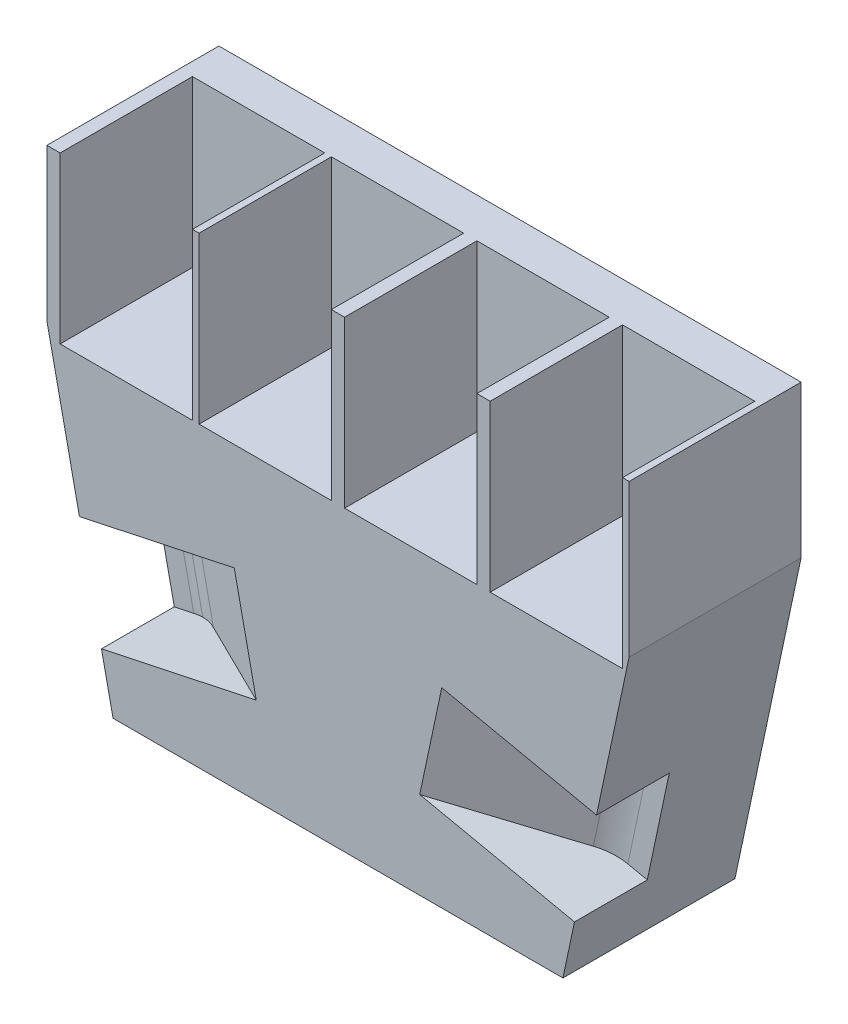
SolidWorks part; units mm, degrees
ref_plane "Front" through (0, 0, 0) normal (0, 0, 1) x (1, 0, 0)
ref_plane "Top" through (0, 0, 0) normal (0, 1, 0) x (1, 0, 0)
ref_plane "Right" through (0, 0, 0) normal (1, 0, 0) x (0, 0, -1)
sketch "草图1" plane through (0, 0, 0) normal (0, 0, 1) x (1, 0, 0)
  line L0 (-34, -24) -> (34, -24)
  line L1 (-44, 46) -> (44, 46)
  line L2 (-44, 46) -> (-44, 23)
  line L4 (44, 46) -> (44, 23)
  line L5 (-66.7553, 0) -> (86.3051, 0) construction
  line L8 (-44, 23) -> (-34, -24)
  line L9 (-44, 23) -> (56.7889, 23) construction
  line L10 (34, -24) -> (44, 23)
  dimension "D1" = 88
  dimension "D3" = 44
  dimension "D4" = 68
  dimension "D5" = 34
  dimension "D6" = 24
extrude "凸台-拉伸1" add sketch "草图1" along normal blind 26
sketch "草图2" plane through (-37.4127, -7.9602, 0) normal (-0.9781, -0.2081, 0) x (0, 0, 1)
  line L0 (13, -16.3989) -> (13, 31.6532) construction
  line L1 (26, -16.3989) -> (0, -16.3989) construction
  line L2 (26, 31.6532) -> (0, 31.6532) construction
  line L3 (0, 0) -> (26, 0)
  line L4 (26, 31.6532) -> (26, -16.3989) construction
sketch "草图3" plane through (0, 0, 0) normal (0, 0, -1) x (-1, 0, 0)
  line L0 (0, -24) -> (0, 47.0389) construction
  line L1 (34, -24) -> (-34, -24) construction
  line L3 (-20, -24) -> (20, -24)
  line L4 (-20, -24) -> (-20, 12)
  line L5 (-20, 12) -> (20, 12)
  line L6 (20, -24) -> (20, 12)
  dimension "D1" = 36
  dimension "D2" = 40
  dimension "D3" = 20
extrude "切除-拉伸4" cut sketch "草图3" against normal blind 20
sketch "草图4" plane through (0, 46, 0) normal (0, 1, 0) x (1, 0, 0)
  line L0 (44, -26) -> (-44, -26) construction
  line L1 (43, -26) -> (23, -26)
  line L2 (43, -26) -> (43, -6)
  line L3 (43, -6) -> (23, -6)
  line L4 (23, -26) -> (23, -6)
  line L5 (44, -26) -> (44, 0) construction
  line L6 (21, -26) -> (1, -26)
  line L7 (21, -26) -> (21, -6)
  line L8 (21, -6) -> (1, -6)
  line L9 (1, -26) -> (1, -6)
  line L10 (-1, -26) -> (-21, -26)
  line L11 (-1, -26) -> (-1, -6)
  line L12 (-1, -6) -> (-21, -6)
  line L13 (-21, -26) -> (-21, -6)
  line L14 (-22, -26) -> (-42, -26)
  line L15 (-22, -26) -> (-22, -6)
  line L16 (-22, -6) -> (-42, -6)
  line L17 (-42, -26) -> (-42, -6)
  dimension "D1" = 20
  dimension "D2" = 21
  dimension "D3" = 20
  dimension "D4" = 20
  dimension "D5" = 20
  dimension "D6" = 2
  dimension "D7" = 2
  dimension "D8" = 20
  dimension "D9" = 20
  dimension "D10" = 20
  dimension "D11" = 21
  dimension "D12" = 20
extrude "切除-拉伸5" cut sketch "草图4" against normal blind 25
sketch3d "3D草图5"
  line L0 (-37.3866, -7.9546, 26.004) -> (-19.9225, -4.2388, 26.004) construction
  line L1 (-37.4127, -7.9602, 0) -> (-37.4127, -7.9602, 26) construction
  line L2 (-37.3866, -7.9546, 26.004) -> (-37.4127, -7.9602, 12.8891) construction
  line L3 (-26.6334, -5.6667, 23.004) -> (-26.6334, -5.6667, 31.004)
  line L4 (-26.6334, -5.6667, 31.004) -> (-34.4583, -7.3315, 31.004)
  arc A0 (-26.6334, -5.6667, 23.004) -> (-34.4583, -7.3315, 31.004) centre (-34.4583, -7.3315, 23.004) ccw
  point P2 (-36.1231, 0.4933, 23.004)
  dimension "D1" = 3
  dimension "D2" = 3
extrude "切除-拉伸3" cut sketch "3D草图5" along direction (0.2081, -0.9781, 0) on the side against the normal mid plane 16
sketch "草图6" plane through (37.4127, -7.9602, 0) normal (0.9781, -0.2081, 0) x (0, 0, -1)
  line L0 (0, 0) -> (-26, 0)
  line L1 (-26, -16.3989) -> (-26, 31.6532) construction
sketch3d "3D草图6"
  line L0 (37.4127, -7.9602, 0) -> (37.4127, -7.9602, 26) construction
  line L2 (37.4127, -7.9602, 26) -> (26.6536, -5.671, 25.9966) construction
  line L3 (34.4784, -7.3358, 14.9991) -> (44.8243, -9.5371, 14.9991)
  line L4 (34.4784, -7.3358, 29) -> (44.8243, -9.5371, 29)
  line L5 (44.8243, -9.5371, 29) -> (44.8243, -9.5371, 14.9991)
  line L6 (26.6536, -5.671, 22.9991) -> (26.6536, -5.671, 29)
  line L7 (26.6536, -5.671, 29) -> (34.4784, -7.3358, 29)
  arc A0 (34.4784, -7.3358, 14.9991) -> (26.6536, -5.671, 22.9991) centre (34.4784, -7.3358, 22.9991) ccw
  point P2 (36.1433, 0.489, 22.9991)
  dimension "D1" = 3
  dimension "D2" = 3
extrude "切除-拉伸6" cut sketch "3D草图6" along direction (0.2081, 0.9781, 0) on the side against the normal mid plane 16
sketch "草图7" plane through (-1.6649, 7.8248, 0) normal (0.2081, -0.9781, 0) x (0.9781, 0.2081, 0)
  line L0 (-38.2502, 0) -> (-38.2502, 26) construction
  line L1 (-38.2502, 26) -> (28.261, 26) construction
  line L2 (-38.2502, 26) -> (-29.5933, 17.3431) construction
  line L3 (-24.5567, 20) -> (-31.2008, 16.1005)
  line L4 (-24.5567, 20) -> (-10.0872, 28.4922)
  line L5 (-10.0872, 28.4922) -> (-33.6713, 30.8426)
  line L6 (-35.2502, 15) -> (-43.2502, 15)
  line L7 (-43.2502, 15) -> (-43.2502, 23)
  arc A0 (-35.2502, 15) -> (-31.2008, 16.1005) centre (-35.2502, 23) ccw
  arc A1 (-33.6713, 30.8426) -> (-43.2502, 23) centre (-35.2502, 23) ccw
  dimension "D3" = 16
  dimension "D1" = 3
  dimension "D2" = 3
extrude "切除-拉伸7" cut sketch "草图7" along normal blind 16
sketch "草图11" plane through (-1.6649, -7.8248, 0) normal (0.2081, 0.9781, 0) x (0.9781, -0.2081, 0)
  line L0 (-28.261, -26) -> (38.2502, -26) construction
  line L1 (38.2502, 0) -> (38.2502, -26) construction
  line L2 (24.5567, -20) -> (31.2008, -16.1005) construction
  line L3 (31.2008, -16.1005) -> (14.3336, -26)
  line L4 (14.3336, -26) -> (32.6666, -30.5713)
  line L5 (35.2502, -15) -> (38.2502, -14.9991)
  line L6 (38.2502, -14.9991) -> (40.4608, -16.9296)
  arc A0 (32.6666, -30.5713) -> (40.4608, -16.9296) centre (35.2502, -23) ccw
  arc A1 (35.2502, -15) -> (31.2008, -16.1005) centre (35.2502, -23) ccw
  dimension "D1" = 3
  dimension "D2" = 3
extrude "切除-拉伸8" cut sketch "草图11" along normal blind 16
